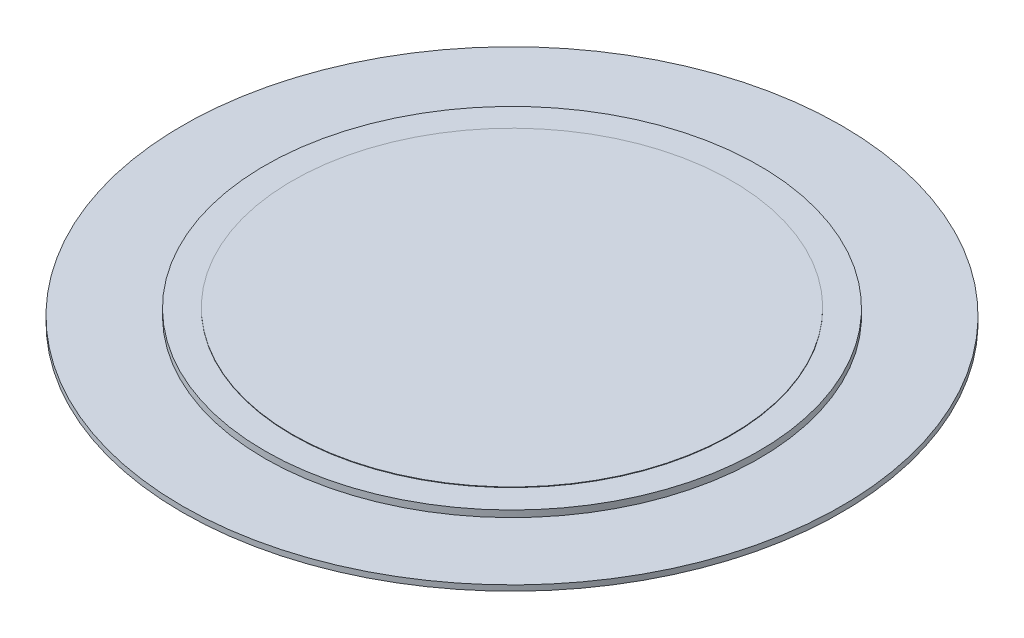
SolidWorks part; units mm, degrees
ref_plane "前视基准面" through (0, 0, 0) normal (0, 0, 1) x (1, 0, 0)
ref_plane "上视基准面" through (0, 0, 0) normal (0, 1, 0) x (1, 0, 0)
ref_plane "右视基准面" through (0, 0, 0) normal (1, 0, 0) x (0, 0, -1)
sketch "草图1" plane through (0, 0, 0) normal (0, 1, 0) x (1, 0, 0)
  circle A0 centre (0, 0) radius 6
  dimension "D1" = 12
extrude "凸台-拉伸1" add sketch "草图1" along normal blind 0.1
sketch "草图2" plane through (0, 0.1, 0) normal (0, 1, 0) x (1, 0, 0)
  circle A0 centre (0, 0) radius 4.5
  dimension "D1" = 9
extrude "凸台-拉伸2" add sketch "草图2" along normal blind 0.12
sketch "草图3" plane through (0, 0.22, 0) normal (0, 1, 0) x (1, 0, 0)
  circle A0 centre (0, 0) radius 4
  dimension "D1" = 8
extrude "凸台-拉伸3" add sketch "草图3" along normal blind 0.01
